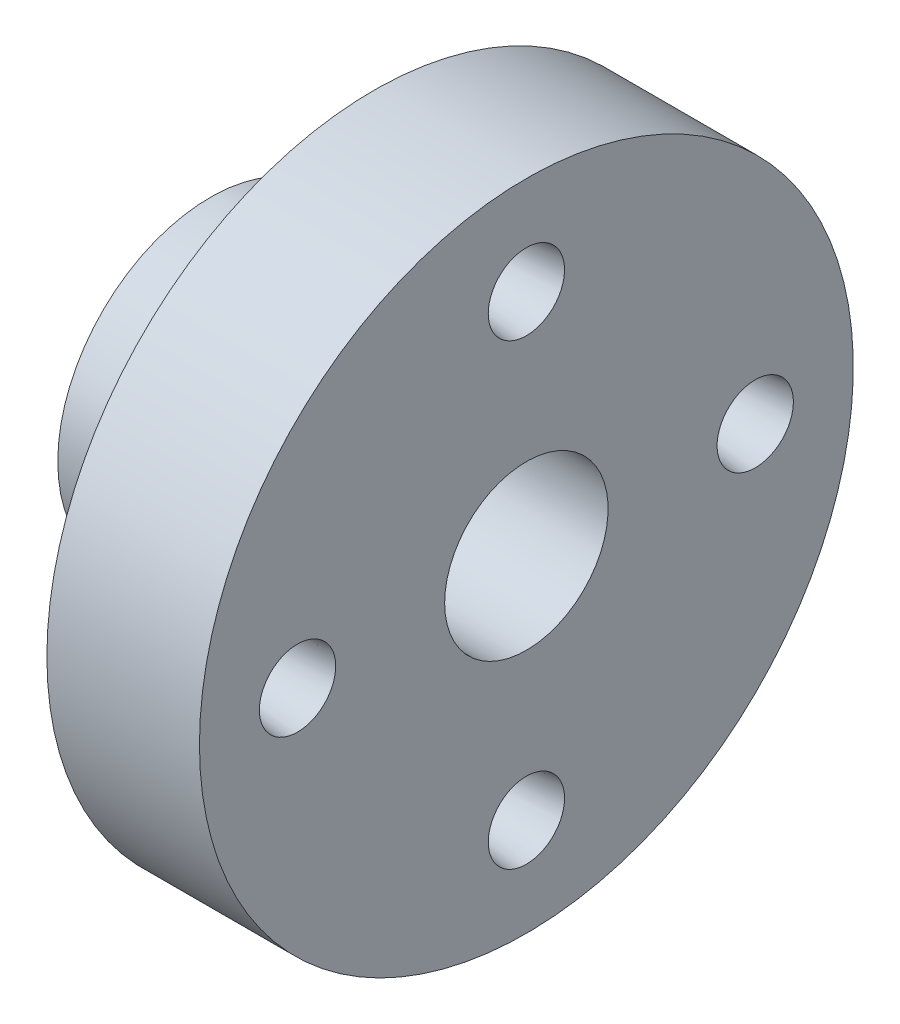
SolidWorks part; units mm, degrees
ref_plane "Спереди" through (0, 0, 0) normal (0, 0, 1) x (1, 0, 0)
ref_plane "Сверху" through (0, 0, 0) normal (0, 1, 0) x (1, 0, 0)
ref_plane "Справа" through (0, 0, 0) normal (1, 0, 0) x (0, 0, -1)
sketch "Эскиз1" plane through (0, 0, 0) normal (0, 0, 1) x (1, 0, 0)
  line L0 (-29, -15) -> (29, -15)
  line L1 (29, -15) -> (29, -60)
  line L2 (29, -60) -> (1, -60)
  line L3 (1, -60) -> (1, -28)
  line L4 (1, -28) -> (-29, -28)
  line L5 (-29, -28) -> (-29, -15)
  line L6 (-29, -15) -> (-29, -15.3621)
  line L7 (-59.7432, 0) -> (59.3811, 0) construction
  point P10 (0, -15)
  dimension "nominalDiameter" = 30
  dimension "D" = 120
  dimension "lpm_" = 58
  dimension "d_st" = 56
  dimension "B" = 28
revolve "Повернуть1" add sketch "Эскиз1" angle 360 about L7
sketch "Эскиз2" [suppressed] plane through (30, 0, 0) normal (1, 0, 0) x (0, 0, -1)
  circle A0 centre (0, 42) radius 14
  circle A1 centre (0, 0) radius 42 construction
  dimension "D0" = 84
  dimension "d_0" = 28
extrude "Вырез-Вытянуть1" [suppressed] cut sketch "Эскиз2" against normal through all contours A0
pattern_circular "Круговой массив1" [suppressed] count 4 over 360
sketch "Эскиз3" plane through (0, 0, 0) normal (0, 0, 1) x (1, 0, 0)
  line L0 (-166.7412, 0) -> (-66.7412, 0) construction
  line L1 (-66.7412, 0) -> (-66.7412, 10) construction
  line L2 (-66.7412, 10) -> (-166.7412, 0) construction
  line L3 (-8.7934, 42) -> (36.6225, 42) construction
  line L5 (29, 42) -> (1, 42)
  line L6 (29, -60) -> (29, 60) construction
  line L7 (1, 42) -> (1, 47.7)
  line L8 (1, 60) -> (1, -60) construction
  line L9 (1, 47.7) -> (16, 47.7)
  line L10 (16, 47.7) -> (29, 49)
  line L11 (29, 49) -> (29, 42)
  line L12 (29, 0) -> (-29, 0) construction
  line L13 (8.9575, 0) -> (34.9339, 0) construction
  dimension "D1" = 100
  dimension "D2" = 10
  dimension "D0" = 84
  dimension "l_nak" = 13
  dimension "d_p" = 14
revolve "Вырез-Повернуть1" cut sketch "Эскиз3" angle 360 about L3
pattern_circular "Круговой массив2" count 4 over 360 about axis through (0, 0, 0) along (1, 0, 0) of "Вырез-Повернуть1"
